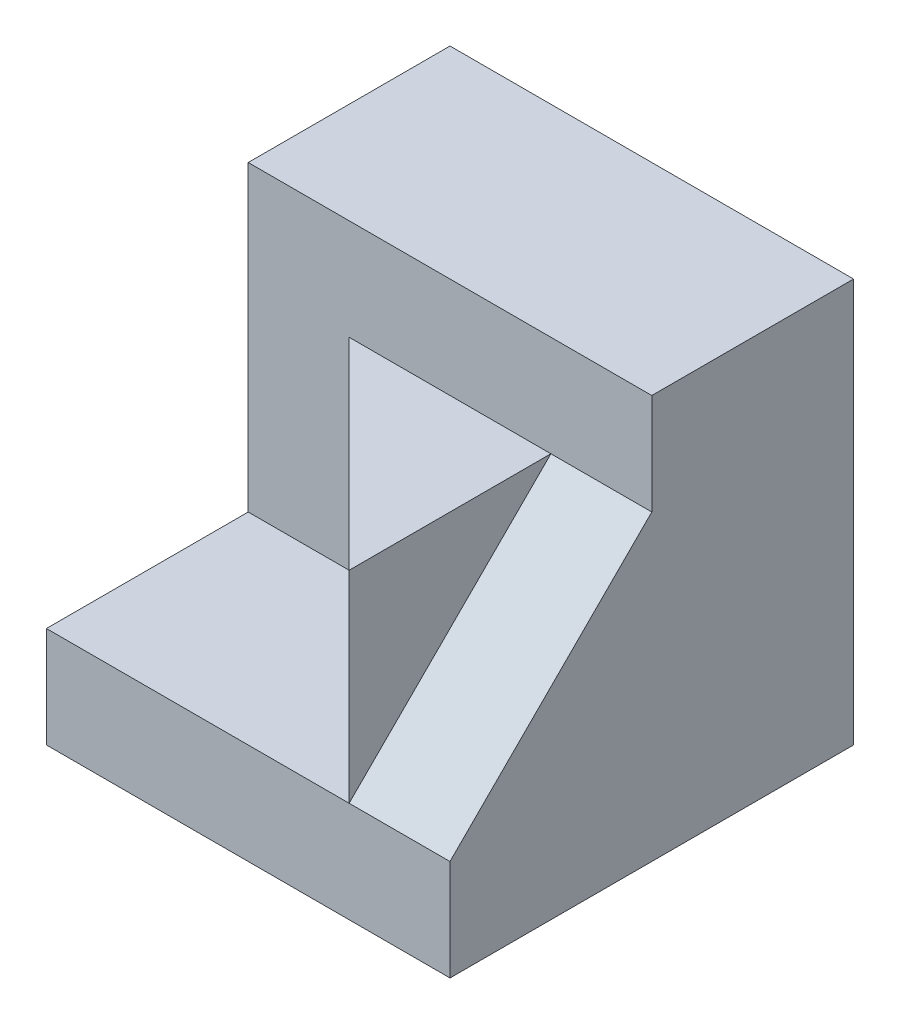
SolidWorks part; units mm, degrees
ref_plane "Front Plane" through (0, 0, 0) normal (0, 0, 1) x (1, 0, 0)
ref_plane "Top Plane" through (0, 0, 0) normal (0, 1, 0) x (1, 0, 0)
ref_plane "Right Plane" through (0, 0, 0) normal (1, 0, 0) x (0, 0, -1)
sketch "Sketch1" plane through (0, 0, 0) normal (1, 0, 0) x (0, 0, -1)
  line L1 (0, 0) -> (4, 0)
  line L2 (0, 0) -> (0, 4)
  line L3 (0, 4) -> (4, 4)
  line L4 (4, 0) -> (4, 4)
  dimension "D1" = 4
  dimension "D2" = 4
extrude "Boss-Extrude1" add sketch "Sketch1" along normal blind 4
sketch "Sketch2" plane through (0, 4, 0) normal (0, 1, 0) x (1, 0, 0)
  line L0 (3, 0) -> (1, 2)
  line L1 (4, 0) -> (0, 0) construction
  line L2 (1, 2) -> (0, 2)
  line L3 (0, 4) -> (0, 0) construction
  line L4 (0, 2) -> (0, 0)
  line L5 (0, 0) -> (3, 0)
  line L6 (4, 4) -> (4, 0) construction
  line L7 (3, 0) -> (4, 0)
  line L8 (3, 0) -> (3, 2)
  line L9 (3, 2) -> (4, 2)
  line L10 (4, 0) -> (4, 2)
  line M5 (0, 4) -> (0, 0)
  line M6 (0, 0) -> (4, 0)
  line M7 (4, 0) -> (4, 4)
  dimension "D1" = 1
  dimension "D2" = 3
  dimension "D3" = 2
extrude "Cut-Extrude1" cut sketch "Sketch2" against normal blind 3 contours L0 L2 M5 M6 | L9 L8 M6 M7
sketch "Sketch4" plane through (0, 4, 0) normal (0, 1, 0) x (1, 0, 0)
  line L1 (4, 0) -> (1, 0)
  line L2 (4, 0) -> (4, 2)
  line L3 (4, 2) -> (1, 2)
  line L4 (1, 0) -> (1, 2)
extrude "Cut-Extrude2" cut sketch "Sketch4" against normal blind 1
sketch "Sketch5" plane through (3, 0, 0) normal (1, 0, 0) x (0, 0, -1)
  line L0 (0, 1) -> (2, 3)
  line L1 (2, 3) -> (2, 1)
  line L2 (2, 1) -> (0, 1)
extrude "Boss-Extrude2" add sketch "Sketch5" along normal blind 1
